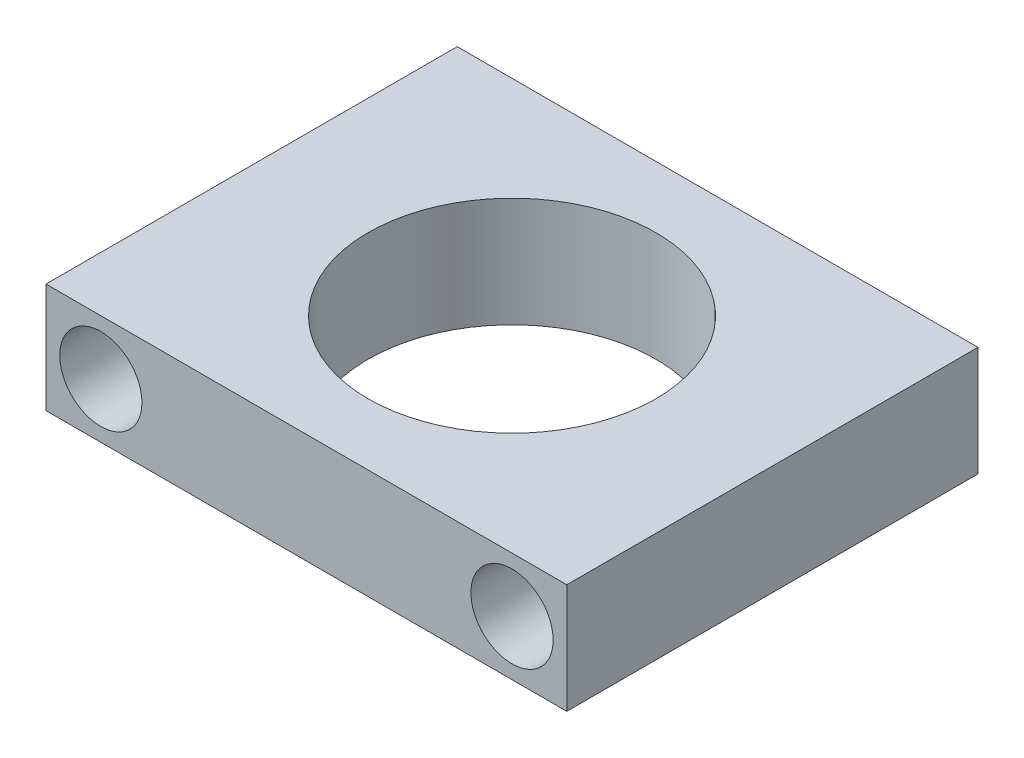
SolidWorks part; units mm, degrees
ref_plane "Front Plane" through (0, 0, 0) normal (0, 0, 1) x (1, 0, 0)
ref_plane "Top Plane" through (0, 0, 0) normal (0, 1, 0) x (1, 0, 0)
ref_plane "Right Plane" through (0, 0, 0) normal (1, 0, 0) x (0, 0, -1)
sketch "Sketch1" plane through (0, 0, 0) normal (0, 1, 0) x (1, 0, 0)
  line L0 (9.5, 15) -> (9.5, 0) construction
  line L1 (0, 0) -> (19, 0)
  line L2 (0, 0) -> (0, 15)
  line L3 (0, 15) -> (19, 15)
  line L4 (19, 0) -> (19, 15)
  line L5 (0, 7.5) -> (19, 7.5) construction
  circle A0 centre (9.5, 7.5) radius 5.25
  dimension "D3" = 10.5
  dimension "D1" = 15
  dimension "D2" = 19
extrude "Boss-Extrude1" add sketch "Sketch1" along normal blind 4
sketch "Sketch2" plane through (0, 0, 0) normal (0, 0, 1) x (1, 0, 0)
  line L0 (0, 2) -> (19, 2) construction
  line L1 (0, 4) -> (0, 0) construction
  line L2 (19, 4) -> (19, 0) construction
  line L3 (17, 4) -> (17, 0) construction
  line L4 (0, 4) -> (19, 4) construction
  line L5 (0, 0) -> (19, 0) construction
  line L6 (2, 4) -> (2, 0) construction
  circle A0 centre (2, 2) radius 1.5
  circle A1 centre (17, 2) radius 1.5
  dimension "D3" = 3
  dimension "D4" = 3
  dimension "D1" = 2
  dimension "D2" = 2
extrude "Cut-Extrude1" cut sketch "Sketch2" against normal blind 15 contours A0 | A1
